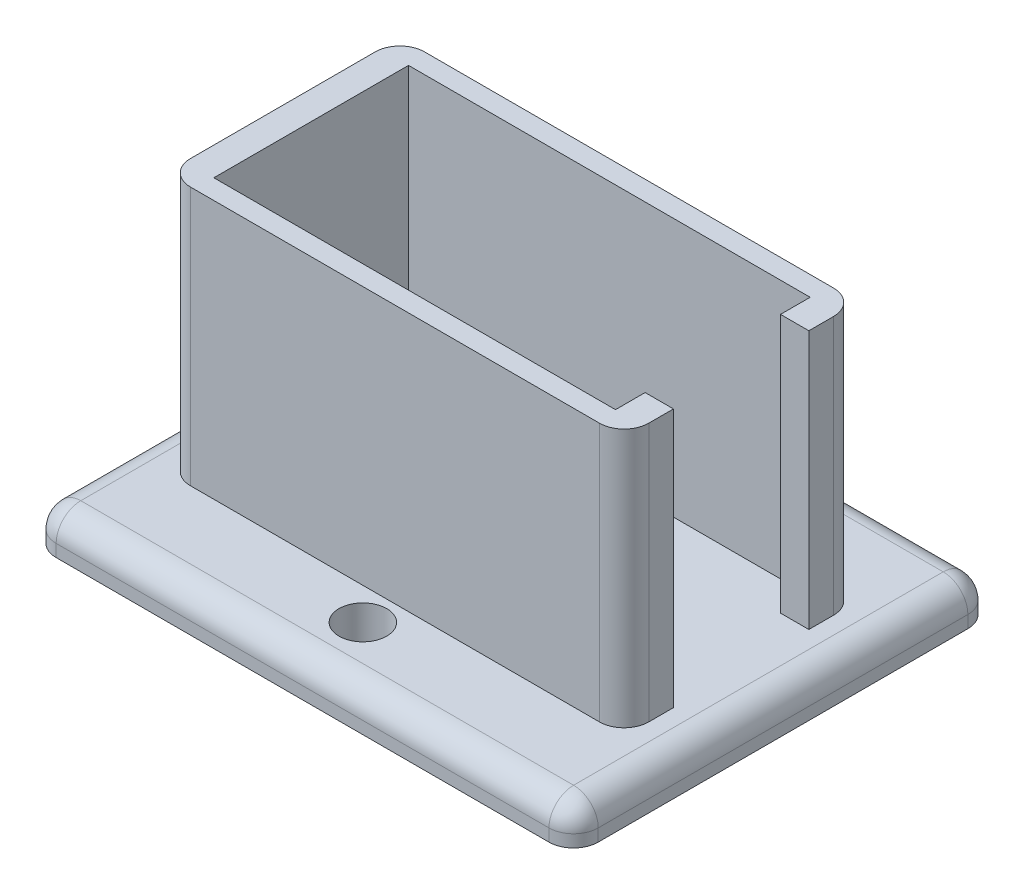
SolidWorks part; units mm, degrees
ref_plane "Front Plane" through (0, 0, 0) normal (0, 0, 1) x (1, 0, 0)
ref_plane "Top Plane" through (0, 0, 0) normal (0, 1, 0) x (1, 0, 0)
ref_plane "Right Plane" through (0, 0, 0) normal (1, 0, 0) x (0, 0, -1)
sketch "Sketch1" plane through (0, 0, 0) normal (0, 1, 0) x (1, 0, 0)
  line L1 (-27.94, -21.59) -> (27.94, -21.59)
  line L2 (-27.94, -21.59) -> (-27.94, 21.59)
  line L3 (-27.94, 21.59) -> (27.94, 21.59)
  line L4 (27.94, -21.59) -> (27.94, 21.59)
  line L5 (-27.94, -21.59) -> (27.94, 21.59) construction
  line L6 (-27.94, 21.59) -> (27.94, -21.59) construction
  point P0 (0, 0)
  dimension "D1" = 43.18
  dimension "D2" = 55.88
extrude "Boss-Extrude1" add sketch "Sketch1" along normal blind 3.81
fillet "Fillet1" radius 2.54 8 edges at (0, 3.81, -21.59) (-27.94, 3.81, 0) (-27.94, 1.905, -21.59) (27.94, 1.905, -21.59) (27.94, 3.81, 0) (0, 3.81, 21.59) (27.94, 1.905, 21.59) (-27.94, 1.905, 21.59)
sketch "Sketch3" plane through (0, 3.81, 0) normal (0, 1, 0) x (1, 0, 0)
  line L1 (-23.622, -12.065) -> (23.622, -12.065)
  line L2 (-23.622, -12.065) -> (-23.622, 12.065)
  line L3 (-23.622, 12.065) -> (23.622, 12.065)
  line L4 (23.622, -12.065) -> (23.622, 12.065)
  line L5 (-23.622, -12.065) -> (23.622, 12.065) construction
  line L6 (-23.622, 12.065) -> (23.622, -12.065) construction
  point P0 (0, 0)
  dimension "D1" = 47.244
  dimension "D2" = 24.13
extrude "Boss-Extrude2" add sketch "Sketch3" along normal blind 26.67
fillet "Fillet2" radius 2.54 4 edges at (23.622, 17.145, 12.065) (23.622, 17.145, -12.065) (-23.622, 17.145, -12.065) (-23.622, 17.145, 12.065)
sketch "Sketch6" plane through (0, 30.48, 0) normal (0, 1, 0) x (1, 0, 0)
  line L1 (-20.701, -10.033) -> (20.701, -10.033)
  line L2 (-20.701, -10.033) -> (-20.701, 10.033)
  line L3 (-20.701, 10.033) -> (20.701, 10.033)
  line L4 (20.701, -10.033) -> (20.701, 10.033)
  line L5 (-20.701, -10.033) -> (20.701, 10.033) construction
  line L6 (-20.701, 10.033) -> (20.701, -10.033) construction
  point P0 (0, 0)
  dimension "D1" = 41.402
  dimension "D2" = 20.066
extrude "Cut-Extrude1" cut sketch "Sketch6" against normal up to surface (26.67 mm away) up to face at (0, 3.81, 0)
sketch "Sketch7" plane through (0, 3.81, 0) normal (0, 1, 0) x (1, 0, 0)
  line L0 (-16.764, 0) -> (16.764, 0) construction
  circle A0 centre (0, 15.3735) radius 2.4619
  circle A1 centre (0, -15.3735) radius 2.4619
  point P2 (0, 0)
extrude "Cut-Extrude2" cut sketch "Sketch7" against normal up to surface (3.81 mm away) contours A0 | A1 up to face at (0, 0, 0)
sketch "Sketch9" plane through (0, 30.48, 0) normal (0, 1, 0) x (1, 0, 0)
  line L0 (23.622, -9.525) -> (23.622, 9.525) construction
  line L1 (19.8432, -6.9779) -> (23.622, -6.9779)
  line L2 (19.8432, -6.9779) -> (19.8432, 6.9779)
  line L3 (19.8432, 6.9779) -> (23.622, 6.9779)
  line L4 (23.622, -6.9779) -> (23.622, 6.9779)
  line L5 (19.8432, -6.9779) -> (23.622, 6.9779) construction
  line L6 (19.8432, 6.9779) -> (23.622, -6.9779) construction
  point P0 (21.7326, 0)
extrude "Cut-Extrude4" cut sketch "Sketch9" against normal up to surface (26.67 mm away) up to face at (0, 3.81, 0)
